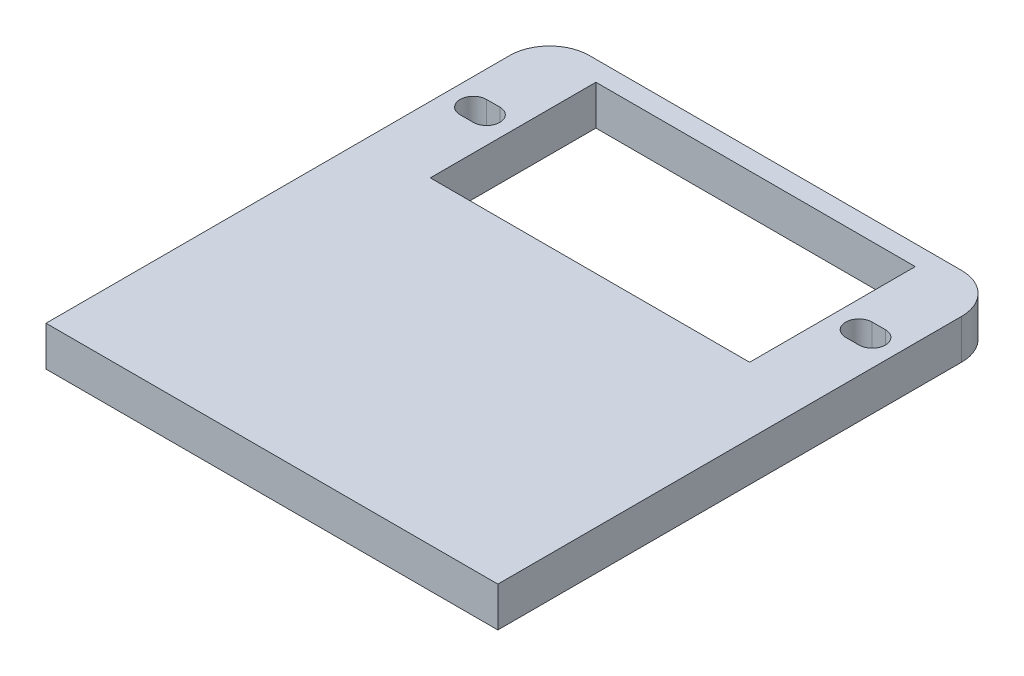
SolidWorks part; units mm, degrees
ref_plane "Plan de face" through (0, 0, 0) normal (0, 0, 1) x (1, 0, 0)
ref_plane "Plan de dessus" through (0, 0, 0) normal (0, 1, 0) x (1, 0, 0)
ref_plane "Plan de droite" through (0, 0, 0) normal (1, 0, 0) x (0, 0, -1)
sketch "Esquisse1" plane through (0, 0, 0) normal (0, 1, 0) x (1, 0, 0)
  line L0 (0, 36.5) -> (-12.05, 36.5)
  line L1 (0, 0) -> (-17.05, 0)
  line L2 (0, 0) -> (0, 38)
  line L3 (0, 38) -> (-17.05, 38)
  line L4 (-17.05, 0) -> (-17.05, 38)
  line L5 (0, 36.5) -> (0, 24)
  line L6 (-12.05, 36.5) -> (-12.05, 24)
  line L7 (0, 24) -> (-12.05, 24)
  line L8 (-15.05, 30.25) -> (-14.05, 30.25) construction
  line L9 (-15.05, 31.25) -> (-14.05, 31.25)
  line L10 (-15.05, 29.25) -> (-14.05, 29.25)
  arc A0 (-15.05, 31.25) -> (-15.05, 29.25) centre (-15.05, 30.25) ccw
  arc A1 (-14.05, 29.25) -> (-14.05, 31.25) centre (-14.05, 30.25) ccw
  point P11 (-14.55, 30.25)
  dimension "D1" = 2
  dimension "D2" = 38
  dimension "D3" = 12.05
  dimension "D4" = 12.5
  dimension "D5" = 24
  dimension "D6" = 6.25
  dimension "D7" = 2
  dimension "D8" = 1
  dimension "D9" = 2
extrude "Boss.-Extru.1" add sketch "Esquisse1" along normal blind 3
mirror "Symétrie1" about plane through (0, 3, 0) normal (-1, 0, 0) of "Boss.-Extru.1"
fillet "Congé1" radius 3 1 edges at (17.05, 1.5, -38)
fillet "Congé2" radius 3 1 edges at (-17.05, 1.5, -38)
